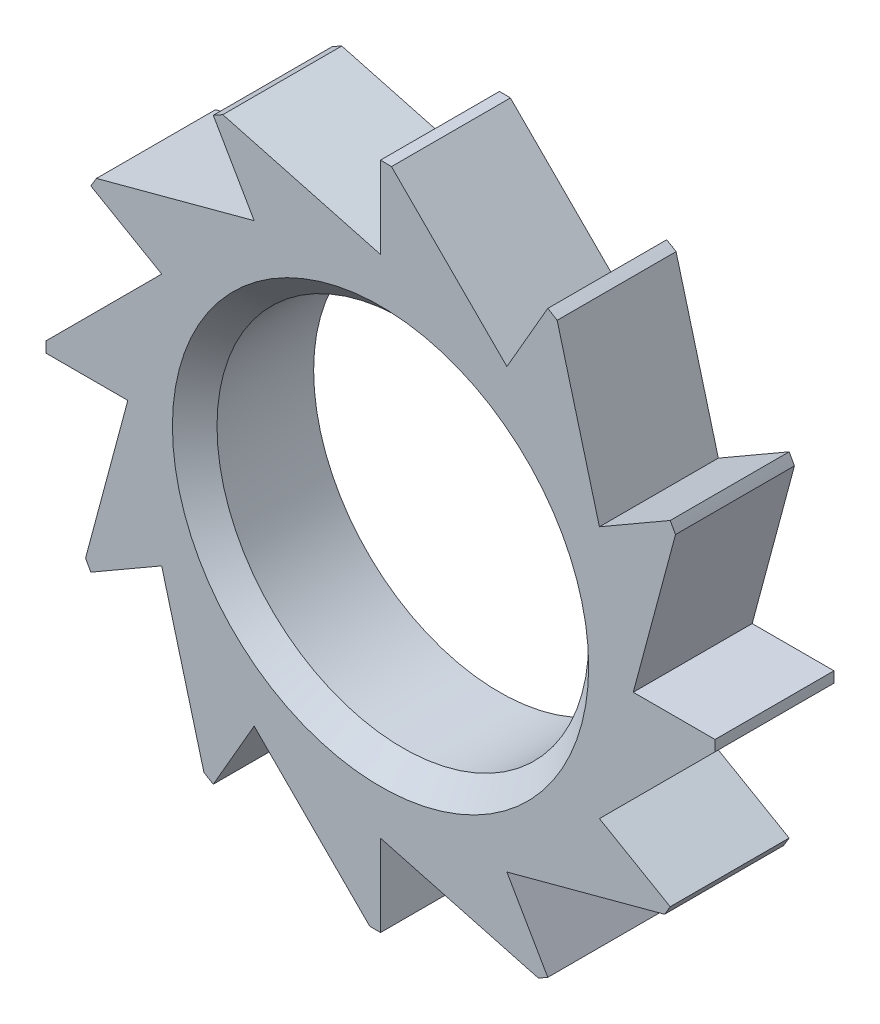
SolidWorks part; units mm, degrees
material "AISI 1020"
ref_plane "Front Plane" through (0, 0, 0) normal (0, 0, 1) x (1, 0, 0)
ref_plane "Top Plane" through (0, 0, 0) normal (0, 1, 0) x (1, 0, 0)
ref_plane "Right Plane" through (0, 0, 0) normal (1, 0, 0) x (0, 0, -1)
sketch "Sketch1" plane through (0, 0, 0) normal (0, 0, 1) x (1, 0, 0)
  circle A0 centre (0, 0) radius 45
  circle A1 centre (0, 0) radius 25
  dimension "D1" = 90
  dimension "D2" = 50
extrude "Boss-Extrude1" add sketch "Sketch1" along normal mid plane 16
chamfer "Chamfer1" distance 3 angle 45 1 edges at (25, 0, 8)
sketch "Sketch2" plane through (0, 0, 8) normal (0, 0, 1) x (1, 0, 0)
  line L0 (0, 45) -> (0, 34)
  line L1 (0, 34) -> (-21.216, 39.6848)
  circle A0 centre (0, 0) radius 45 construction
  arc A1 (0, 45) -> (-21.216, 39.6848) centre (0, 0) ccw
  dimension "D1" = 11
  dimension "D2" = 75
extrude "Cut-Extrude1" cut sketch "Sketch2" against normal through all both and the other way through all
pattern_circular "CirPattern1" count 12 over 360 about axis through (0, 0, 0) along (0, 0, 1) of "Cut-Extrude1"
